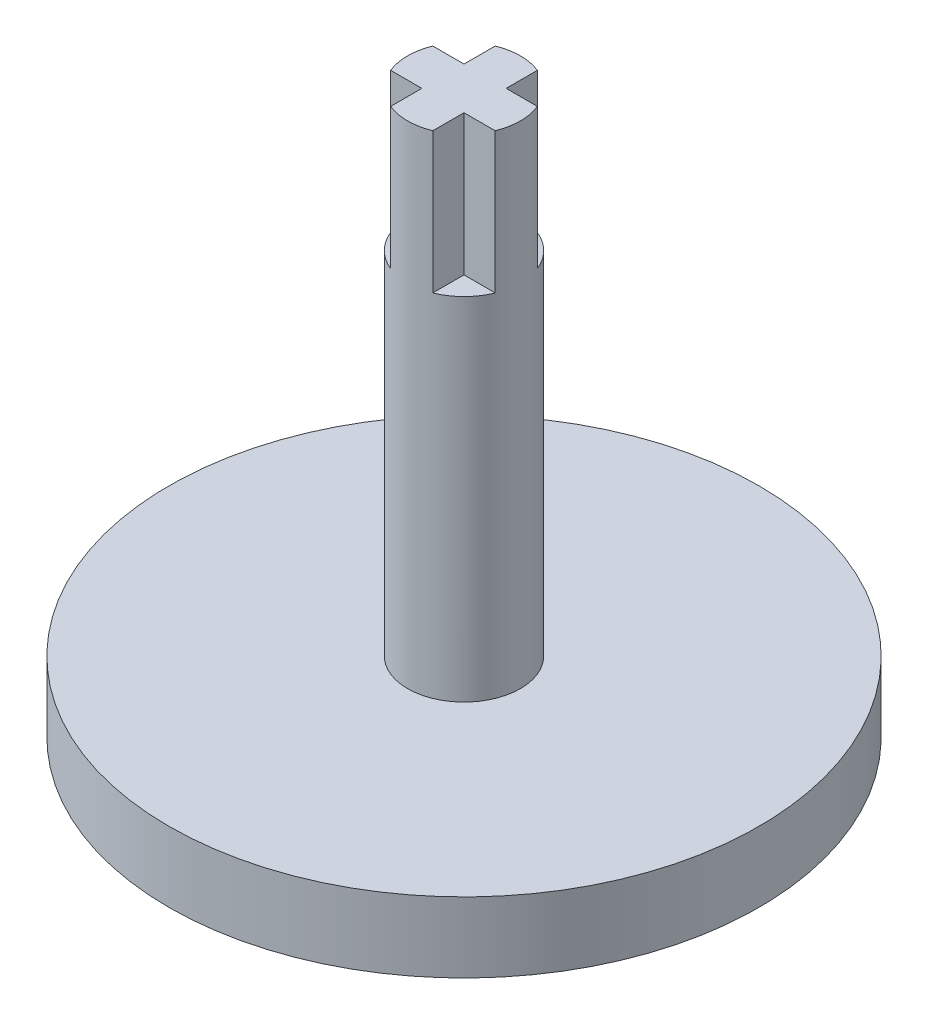
SolidWorks part; units mm, degrees
ref_plane "정면" through (0, 0, 0) normal (0, 0, 1) x (1, 0, 0)
ref_plane "윗면" through (0, 0, 0) normal (0, 1, 0) x (1, 0, 0)
ref_plane "우측면" through (0, 0, 0) normal (1, 0, 0) x (0, 0, -1)
sketch "스케치1" plane through (0, 0, 0) normal (0, 1, 0) x (1, 0, 0)
  circle A0 centre (0, 0) radius 21
  dimension "D1" = 42
extrude "보스-돌출1" add sketch "스케치1" along normal blind 5
sketch "스케치3" plane through (0, 0, 0) normal (0, -1, 0) x (1, 0, 0)
  circle A0 centre (0, 0) radius 6.05
  dimension "D1" = 12.1
extrude "컷-돌출2" cut sketch "스케치3" against normal blind 3.5
sketch "스케치4" plane through (0, 5, 0) normal (0, 1, 0) x (1, 0, 0)
  circle A0 centre (0, 0) radius 4.015
  dimension "D1" = 8.03
extrude "보스-돌출2" add sketch "스케치4" along normal blind 25
sketch "스케치8" plane through (0, 5, 0) normal (0, 1, 0) x (1, 0, 0)
  circle A0 centre (0, 14.5) radius 5.15
  dimension "D1" = 10.3
  dimension "D2" = 14.5
sketch "스케치12" plane through (0, 0, 0) normal (0, -1, 0) x (1, 0, 0)
  circle A0 centre (0, -14.5) radius 5.15 construction
  circle A1 centre (0, 0) radius 21
  circle A2 centre (0, 0) radius 21
  circle A3 centre (0, -14.5) radius 5.15
  dimension "D1" = 0
extrude "컷-돌출6" cut sketch "스케치12" against normal blind 3 contours A3
pattern_circular "원형 패턴1" count 8 over 360 about axis through (0, 0, 0) along (0, 1, 0) of "컷-돌출6"
sketch "스케치13" plane through (0, 30, 0) normal (0, 1, 0) x (1, 0, 0)
  line L0 (-1.5, 3.7243) -> (-1.5, -3.7243)
  line L1 (3.7243, 1.5) -> (-3.7243, 1.5)
  line L2 (1.5, -3.7243) -> (1.5, 3.7243)
  line L3 (-3.7243, -1.5) -> (3.7243, -1.5)
  circle A0 centre (0, 0) radius 4.015 construction
  circle A1 centre (0, 0) radius 4.015
  point P14 (0, 0)
  circle M2 centre (0, 0) radius 4.015
  dimension "D1" = 1.5
  dimension "D2" = 4
extrude "보스-돌출3" add sketch "스케치13" along normal blind 10 contours L1 L2 L0 M2 | L3 L0 L1 M2 | L0 L3 L2 L1 | L3 L0 L2 M2 | L2 L3 L1 M2
